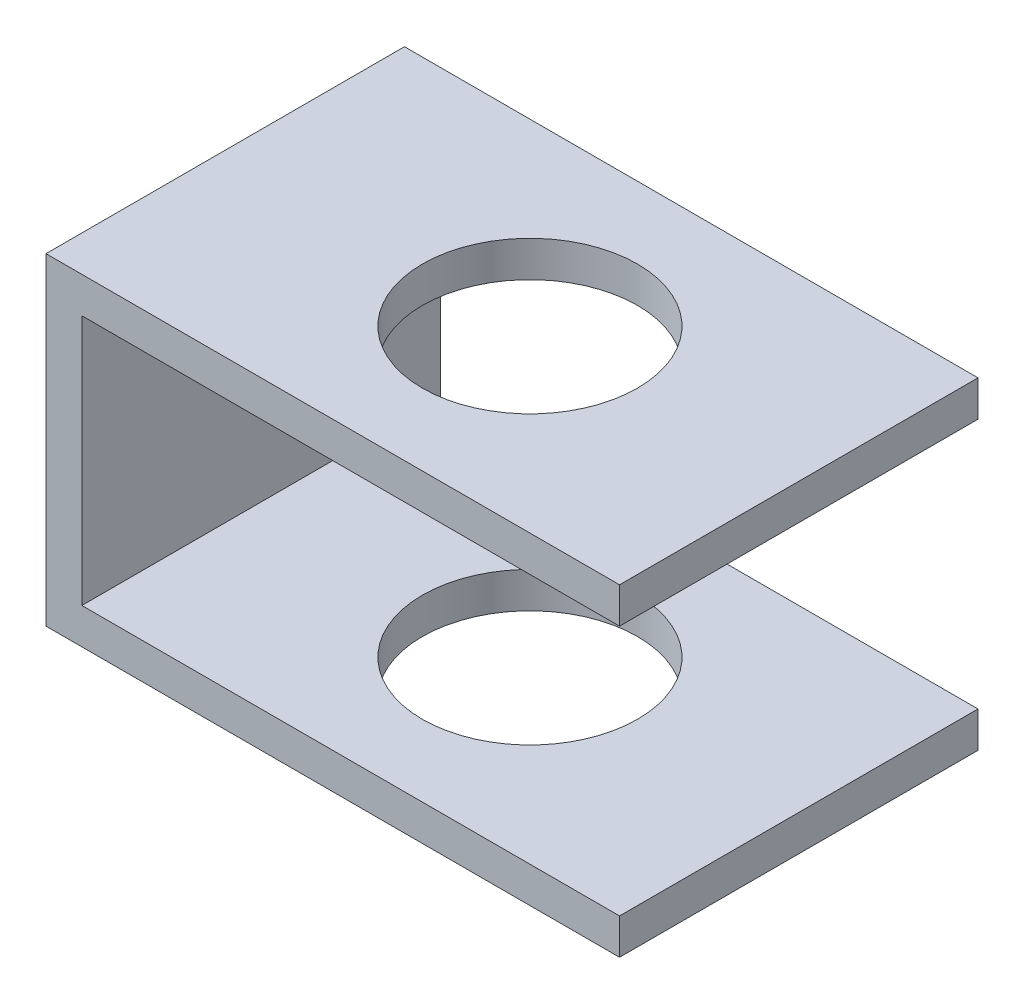
SolidWorks part; units mm, degrees
ref_plane "Front Plane" through (0, 0, 0) normal (0, 0, 1) x (1, 0, 0)
ref_plane "Top Plane" through (0, 0, 0) normal (0, 1, 0) x (1, 0, 0)
ref_plane "Right Plane" through (0, 0, 0) normal (1, 0, 0) x (0, 0, -1)
sketch "Sketch4" plane through (0, 0, 0) normal (0, 0, 1) x (1, 0, 0)
  line L1 (0, 0) -> (1.6, 0)
  line L2 (0, 0) -> (0, -0.9)
  line L3 (0, -0.9) -> (1.6, -0.9)
  line L4 (1.6, 0) -> (1.6, -0.9)
  dimension "D1" = 1.6
  dimension "D2" = 0.9
extrude "Boss-Extrude3" add sketch "Sketch4" along normal blind 1
sketch "Sketch6" plane through (0, 0, 0) normal (0, 1, 0) x (1, 0, 0)
  line L0 (-0.7861, 0) -> (0.7861, 0) construction
  line L1 (1.6, -1) -> (1.6, 0) construction
  circle A0 centre (0.85, -0.5) radius 0.3
  dimension "D1" = 0.5
  dimension "D2" = 0.75
extrude "Cut-Extrude2" cut sketch "Sketch6" against normal blind 1
sketch "Sketch7" plane through (1.6, 0, 0) normal (1, 0, 0) x (0, 0, -1)
  line L0 (-1, -0.9) -> (-1, 0) construction
  line L1 (-1, -0.1) -> (0, -0.1)
  line L2 (-1, -0.1) -> (-1, -0.8)
  line L3 (-1, -0.8) -> (0, -0.8)
  line L4 (0, -0.1) -> (0, -0.8)
  line L5 (0, -0.9) -> (0, 0) construction
  line L6 (-1, 0) -> (0, 0) construction
  dimension "D1" = 0.7
  dimension "D2" = 0.1
extrude "Cut-Extrude3" cut sketch "Sketch7" against normal blind 1.5
